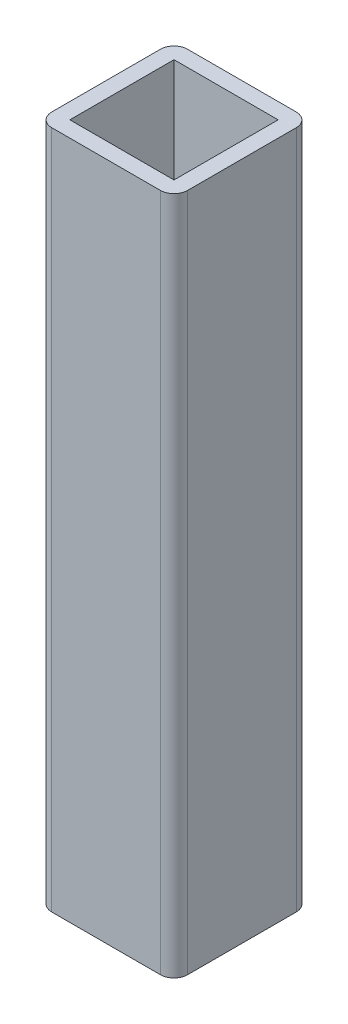
SolidWorks part; units mm, degrees
ref_plane "Front Plane" through (0, 0, 0) normal (0, 0, 1) x (1, 0, 0)
ref_plane "Top Plane" through (0, 0, 0) normal (0, 1, 0) x (1, 0, 0)
ref_plane "Right Plane" through (0, 0, 0) normal (1, 0, 0) x (0, 0, -1)
sketch "Sketch1" plane through (0, 0, 0) normal (0, 1, 0) x (1, 0, 0)
  line L1 (12, 15) -> (-12, 15)
  line L2 (15, 12) -> (15, -12)
  line L3 (12, -15) -> (-12, -15)
  line L4 (-15, 12) -> (-15, -12)
  line L5 (15, 15) -> (-15, -15) construction
  line L6 (15, -15) -> (-15, 15) construction
  line L7 (11.5, 11.5) -> (-11.5, 11.5)
  line L8 (11.5, 11.5) -> (11.5, -11.5)
  line L9 (11.5, -11.5) -> (-11.5, -11.5)
  line L10 (-11.5, 11.5) -> (-11.5, -11.5)
  line L11 (11.5, 11.5) -> (-11.5, -11.5) construction
  line L12 (11.5, -11.5) -> (-11.5, 11.5) construction
  arc A0 (12, 15) -> (15, 12) centre (12, 12) cw
  arc A1 (15, -12) -> (12, -15) centre (12, -12) cw
  arc A2 (-12, -15) -> (-15, -12) centre (-12, -12) cw
  arc A3 (-12, 15) -> (-15, 12) centre (-12, 12) ccw
  point P0 (0, 0)
  point P1 (0, 0)
  dimension "D4" = 3
  dimension "D1" = 30
  dimension "D2" = 30
  dimension "D3" = 23
extrude "Boss-Extrude1" add sketch "Sketch1" along normal blind 150
